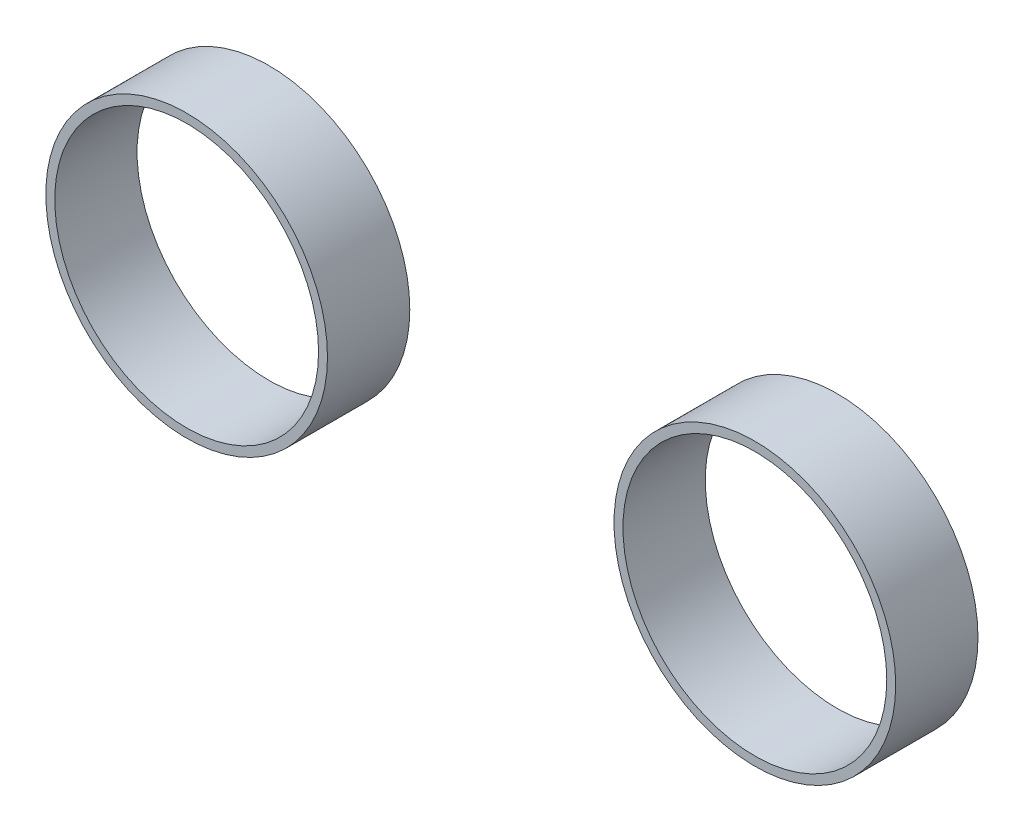
SolidWorks part; units mm, degrees
material "Velcro"
ref_plane "Front Plane" through (0, 0, 0) normal (0, 0, 1) x (1, 0, 0)
ref_plane "Top Plane" through (0, 0, 0) normal (0, 1, 0) x (1, 0, 0)
ref_plane "Right Plane" through (0, 0, 0) normal (1, 0, 0) x (0, 0, -1)
sketch "Sketch1" plane through (0, 0, 0) normal (0, 0, 1) x (1, 0, 0)
  circle A0 centre (1715.9805, -423.3823) radius 69.4 construction
  circle A1 centre (1715.9805, -423.3823) radius 65 construction
  circle A2 centre (1435.9805, -423.3823) radius 69.4 construction
  circle A3 centre (1435.9805, -423.3823) radius 65 construction
  circle A4 centre (1715.9805, -423.3823) radius 69.4
  circle A5 centre (1715.9805, -423.3823) radius 65
  circle A6 centre (1435.9805, -423.3823) radius 69.4
  circle A7 centre (1435.9805, -423.3823) radius 65
extrude "Boss-Extrude1" add sketch "Sketch1" against normal blind 40.56
